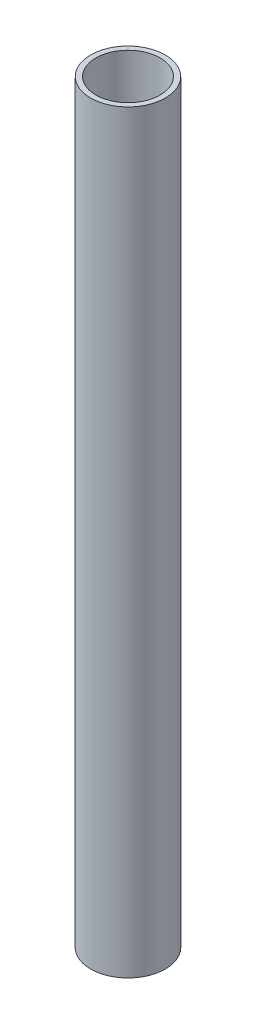
SolidWorks part; units mm, degrees
material "PVC Rigid"
ref_plane "Front Plane" through (0, 0, 0) normal (0, 0, 1) x (1, 0, 0)
ref_plane "Top Plane" through (0, 0, 0) normal (0, 1, 0) x (1, 0, 0)
ref_plane "Right Plane" through (0, 0, 0) normal (1, 0, 0) x (0, 0, -1)
sketch "Sketch1" plane through (0, 0, 0) normal (0, 1, 0) x (1, 0, 0)
  circle A0 centre (0, 0) radius 25.9969
  circle A1 centre (0, 0) radius 30.1625
  dimension "D1" = 51.9938
  dimension "D2" = 60.325
extrude "Boss-Extrude1" add sketch "Sketch1" along normal blind 609.6
